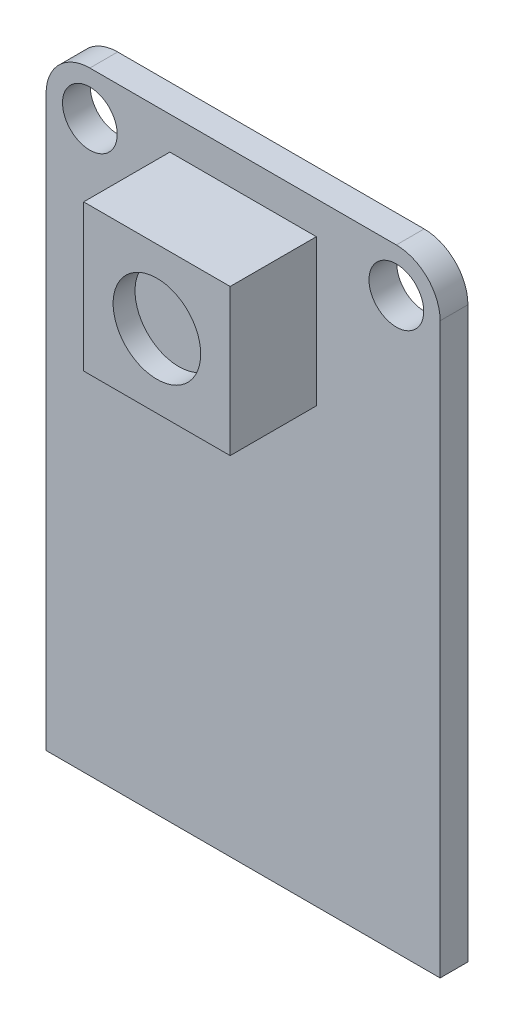
SolidWorks part; units mm, degrees
ref_plane "Front Plane" through (0, 0, 0) normal (0, 0, 1) x (1, 0, 0)
ref_plane "Top Plane" through (0, 0, 0) normal (0, 1, 0) x (1, 0, 0)
ref_plane "Right Plane" through (0, 0, 0) normal (1, 0, 0) x (0, 0, -1)
sketch "Sketch1" plane through (0, 0, 0) normal (0, 0, 1) x (1, 0, 0)
  line L1 (-11.43, -17.78) -> (11.43, -17.78)
  line L2 (-11.43, -17.78) -> (-11.43, 17.78)
  line L3 (-11.43, 17.78) -> (11.43, 17.78)
  line L4 (11.43, -17.78) -> (11.43, 17.78)
  line L5 (-11.43, -17.78) -> (11.43, 17.78) construction
  line L6 (-11.43, 17.78) -> (11.43, -17.78) construction
  point P0 (0, 0)
  dimension "D1" = 35.56
  dimension "D2" = 22.86
extrude "Boss-Extrude1" add sketch "Sketch1" along normal blind 1.6129
fillet "Fillet1" radius 2.54 2 edges at (11.43, 17.78, 0.8065) (-11.43, 17.78, 0.8065)
sketch "Sketch2" plane through (0, 0, 1.6129) normal (0, 0, 1) x (1, 0, 0)
  line L0 (-11.43, -17.78) -> (11.43, -17.78) construction
  line L1 (-4.25, 15.875) -> (4.25, 15.875)
  line L2 (-4.25, 15.875) -> (-4.25, 7.375)
  line L3 (-4.25, 7.375) -> (4.25, 7.375)
  line L4 (4.25, 15.875) -> (4.25, 7.375)
  line L5 (0, 0) -> (0, 15.875) construction
  point P9 (0, 7.375)
  dimension "D1" = 8.5
  dimension "D2" = 8.5
  dimension "D3" = 33.655
extrude "Boss-Extrude2" add sketch "Sketch2" along normal blind 5
sketch "Sketch3" plane through (0, 0, 1.6129) normal (0, 0, 1) x (1, 0, 0)
  circle A0 centre (-8.89, 15.24) radius 1.5875
  circle A1 centre (8.89, 15.24) radius 1.5875
  dimension "D1" = 3.175
  dimension "D2" = 3.175
extrude "Cut-Extrude1" cut sketch "Sketch3" against normal up to next
sketch "Sketch4" plane through (0, 0, 6.6129) normal (0, 0, 1) x (1, 0, 0)
  line L0 (0, 7.375) -> (0, 15.875) construction
  line L1 (-4.25, 7.375) -> (4.25, 7.375) construction
  line L2 (4.25, 15.875) -> (-4.25, 15.875) construction
  line L3 (-4.25, 11.625) -> (4.25, 11.625) construction
  line L4 (-4.25, 15.875) -> (-4.25, 7.375) construction
  line L5 (4.25, 7.375) -> (4.25, 15.875) construction
  circle A0 centre (0, 11.625) radius 2.54
  dimension "D1" = 5.08
extrude "Cut-Extrude2" cut sketch "Sketch4" against normal blind 1.27
